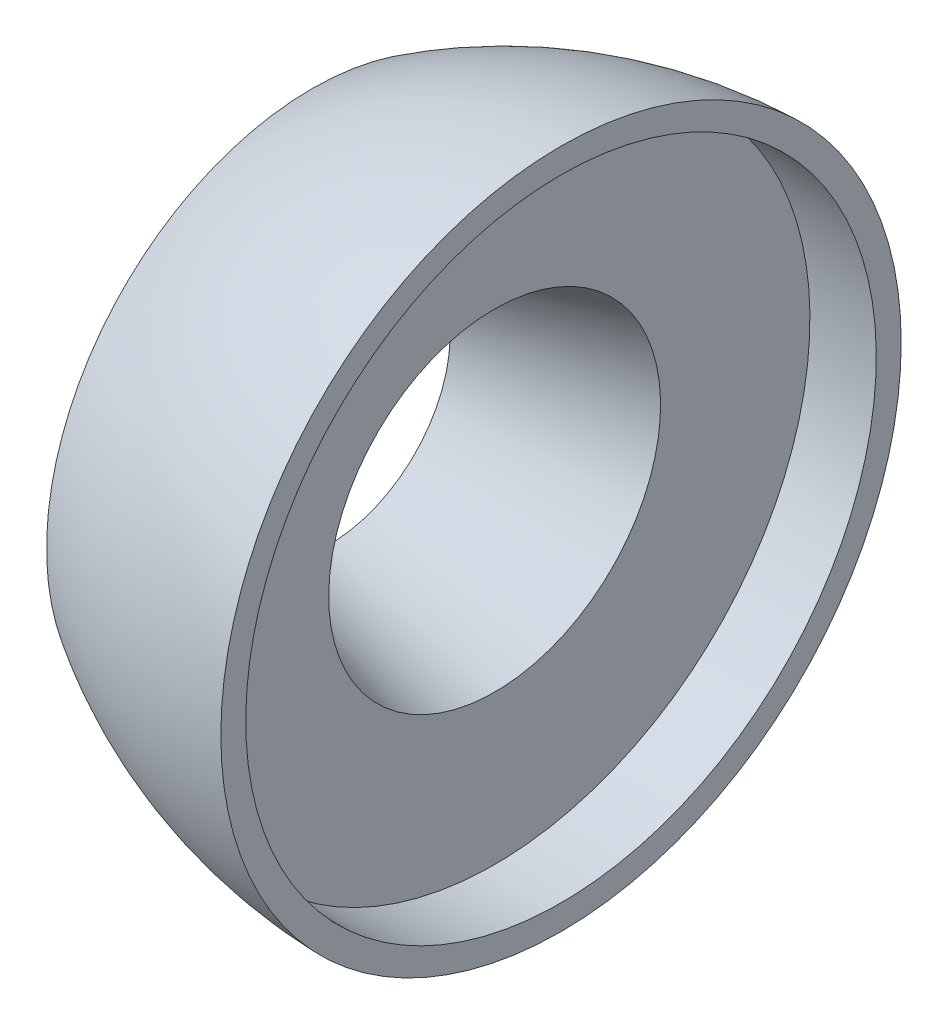
SolidWorks part; units mm, degrees
material "1345 Alloy"
ref_plane "Front Plane" through (0, 0, 0) normal (0, 0, 1) x (1, 0, 0)
ref_plane "Top Plane" through (0, 0, 0) normal (0, 1, 0) x (1, 0, 0)
ref_plane "Right Plane" through (0, 0, 0) normal (1, 0, 0) x (0, 0, -1)
sketch "Sketch1" plane through (0, 0, 0) normal (0, 0, 1) x (1, 0, 0)
  line L0 (0, 0) -> (-5.5, 0) construction
  line L1 (-5, 3.6603) -> (0, 5)
  line L2 (0, 5) -> (0, 9.5)
  line L3 (2, 9.5) -> (0, 9.5)
  line L5 (2, 9.5) -> (2, 10.25)
  line L6 (-5, 3.6603) -> (-5, 5)
  line L7 (-5, 5) -> (-5.5, 5)
  line L8 (-5.5, 5) -> (-5.5, 8)
  arc A1 (2, 10.25) -> (-5.5, 8) centre (2.4108, -4.7444) ccw
  dimension "D13" = 15
  dimension "D1" = 15
  dimension "D2" = 10
  dimension "D4" = 19
  dimension "D5" = 2
  dimension "D8" = 0.5
  dimension "D9" = 10
  dimension "D10" = 5.5
  dimension "D11" = 16
  dimension "D12" = 20.5
revolve "Revolve1" add sketch "Sketch1" angle 360 about L0
ref_axis "Axis1" through (-5.5, 0, 0) along (1, 0, 0)
sketch "Sketch2" plane through (0, 0, 0) normal (0, 0, 1) x (1, 0, 0)
  line L0 (-6.7, 0) -> (-6.7, 0.5) construction
  line L1 (-6.7, 0.5) -> (-6.7, 12.5)
  arc A0 (-6.7, 0.5) -> (-6.7, 12.5) centre (-20.4477, 6.5) ccw
  dimension "D3" = 15
  dimension "D1" = 6.7
  dimension "D2" = 6.5
  dimension "D4" = 12
revolve "Cut-Revolve1" cut sketch "Sketch2" angle 360 about L0
pattern_circular "CirPattern1" count 36 over 360 about axis through (-5.5, 0, 0) along (1, 0, 0) of "Cut-Revolve1"
